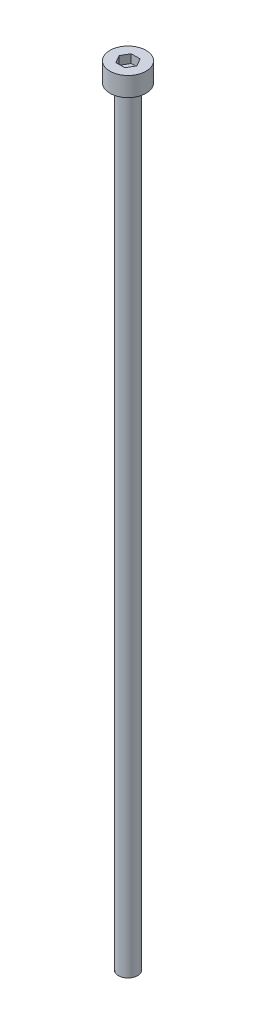
SolidWorks part; units mm, degrees
material "AISI 304"
ref_plane "前视基准面" through (0, 0, 0) normal (0, 0, 1) x (1, 0, 0)
ref_plane "上视基准面" through (0, 0, 0) normal (0, 1, 0) x (1, 0, 0)
ref_plane "右视基准面" through (0, 0, 0) normal (1, 0, 0) x (0, 0, -1)
sketch "草图1" plane through (0, 0, 0) normal (0, 1, 0) x (1, 0, 0)
  circle A0 centre (0, 0) radius 2.35
  dimension "D1" = 4.7
extrude "杯头" add sketch "草图1" along normal blind 2.5
sketch "草图2" plane through (0, 2.5, 0) normal (0, 1, 0) x (1, 0, 0)
  line L1 (1.1547, 0) -> (0.5774, 1)
  line L2 (0.5774, 1) -> (-0.5774, 1)
  line L3 (-0.5774, 1) -> (-1.1547, 0)
  line L4 (-1.1547, 0) -> (-0.5774, -1)
  line L5 (-0.5774, -1) -> (0.5774, -1)
  line L6 (0.5774, -1) -> (1.1547, 0)
  circle A0 centre (0, 0) radius 1 construction
  dimension "D1" = 2
extrude "内六角口" cut sketch "草图2" against normal blind 1.1
sketch "草图3" plane through (0, 0, 0) normal (0, -1, 0) x (1, 0, 0)
  circle A0 centre (0, 0) radius 1.25
  dimension "D1" = 2.5
extrude "螺纹长" add sketch "草图3" along normal blind 100
